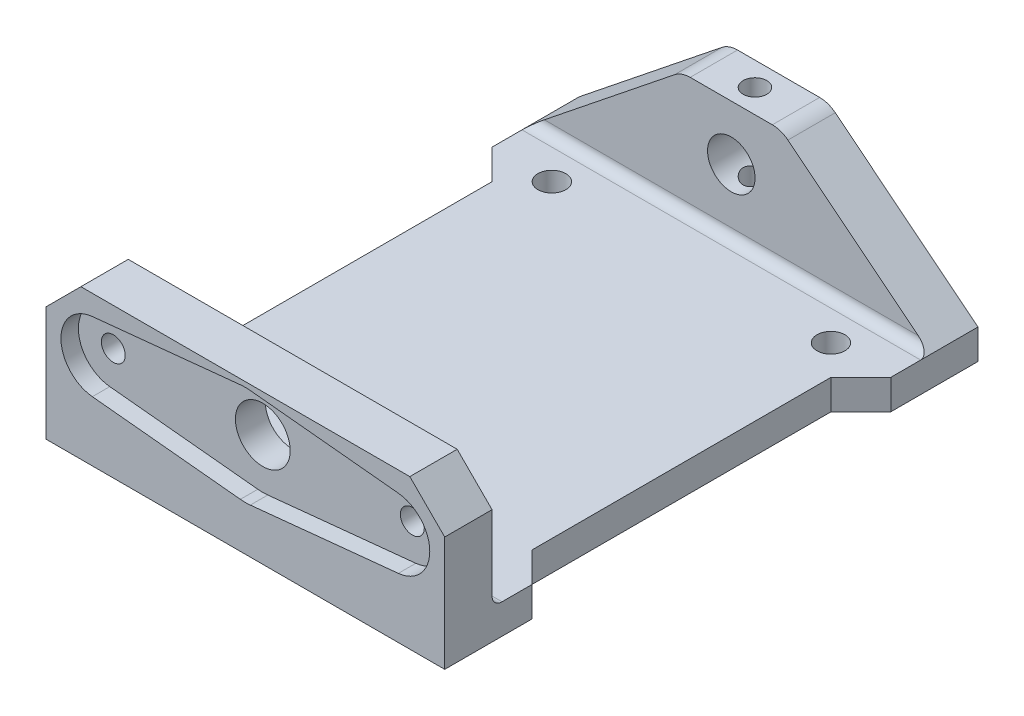
SolidWorks part; units mm, degrees
ref_plane "Front Plane" through (0, 0, 0) normal (0, 0, 1) x (1, 0, 0)
ref_plane "Top Plane" through (0, 0, 0) normal (0, 1, 0) x (1, 0, 0)
ref_plane "Right Plane" through (0, 0, 0) normal (1, 0, 0) x (0, 0, -1)
sketch "Sketch1" plane through (0, 0, 0) normal (0, 1, 0) x (1, 0, 0)
  line L1 (-14, 18) -> (14, 18)
  line L2 (-14, 18) -> (-14, -18)
  line L3 (-14, -18) -> (14, -18)
  line L4 (14, 18) -> (14, -18)
  line L5 (-14, 18) -> (14, -18) construction
  line L6 (-14, -18) -> (14, 18) construction
  line L7 (-20, 22) -> (20, 22)
  line L8 (-20, 22) -> (-20, -22)
  line L9 (-20, -22) -> (20, -22)
  line L10 (20, 22) -> (20, -22)
  line L11 (-20, 22) -> (20, -22) construction
  line L12 (-20, -22) -> (20, 22) construction
  circle A0 centre (-14, 18) radius 1.4
  circle A1 centre (14, 18) radius 1.4
  circle A2 centre (-14, -18) radius 1.4
  circle A3 centre (14, -18) radius 1.4
  point P0 (0, 0)
  point P6 (0, 0)
  dimension "D3" = 2.8
  dimension "D4" = 2.8
  dimension "D5" = 2.8
  dimension "D6" = 2.8
  dimension "D1" = 36
  dimension "D2" = 28
  dimension "D7" = 40
  dimension "D8" = 44
extrude "Boss-Extrude1" add sketch "Sketch1" along normal blind 3 contours L10 L7 L8 L9 A3 L3 A2 L2 A0 L1 A1 L4 | A3 L4 A1 L1 A0 L2 A2 L3
sketch "Sketch2" plane through (0, 0, 22) normal (0, 0, 1) x (1, 0, 0)
  line L0 (20, 3) -> (20, 0) construction
  line L1 (-20, 0) -> (20, 0)
  line L2 (-20, 0) -> (-20, 15)
  line L3 (-20, 15) -> (20, 15)
  line L4 (20, 0) -> (20, 15)
  dimension "D1" = 15
extrude "Boss-Extrude2" add sketch "Sketch2" along normal blind 4.75
sketch "Sketch3" plane through (0, 0, -22) normal (0, 0, -1) x (-1, 0, 0)
  line L1 (-20, 0) -> (20, 0)
  line L2 (-20, 0) -> (-20, 15)
  line L3 (-20, 15) -> (20, 15)
  line L4 (20, 0) -> (20, 15)
extrude "Boss-Extrude3" add sketch "Sketch3" along normal blind 4.75
sketch "Sketch4" plane through (0, 0, 26.75) normal (0, 0, 1) x (1, 0, 0)
  line L0 (-20, 9.5) -> (20, 9.5) construction
  line L1 (-20, 15) -> (-20, 0) construction
  line L2 (20, 0) -> (20, 15) construction
  line L3 (20, 15) -> (-20, 15) construction
  line L4 (-15.25, 11.9875) -> (-0.4, 13.4799)
  line L5 (-15.25, 7.0125) -> (-0.4, 5.5201)
  line L6 (0.4, 5.5201) -> (15.25, 7.0125)
  line L7 (15.25, 11.9875) -> (0.4, 13.4799)
  line L8 (15.35, 12.9825) -> (0.5, 14.4749)
  line L9 (-15.35, 12.9825) -> (-0.5, 14.4749)
  line L10 (-15.35, 6.0175) -> (-0.5, 4.5251)
  line L11 (0.5, 4.5251) -> (15.35, 6.0175)
  arc A0 (0.4, 13.4799) -> (-0.4, 13.4799) centre (0, 9.5) ccw
  arc A1 (15.25, 7.0125) -> (15.25, 11.9875) centre (15, 9.5) ccw
  arc A2 (-15.25, 11.9875) -> (-15.25, 7.0125) centre (-15, 9.5) ccw
  arc A3 (-0.4, 5.5201) -> (0.4, 5.5201) centre (0, 9.5) ccw
  arc A4 (15.35, 6.0175) -> (15.35, 12.9825) centre (15, 9.5) ccw
  arc A5 (0.5, 14.4749) -> (-0.5, 14.4749) centre (0, 9.5) ccw
  arc A6 (-15.35, 12.9825) -> (-15.35, 6.0175) centre (-15, 9.5) ccw
  arc A7 (-0.5, 4.5251) -> (0.5, 4.5251) centre (0, 9.5) ccw
  dimension "D2" = 8
  dimension "D3" = 5
  dimension "D4" = 5
  dimension "D1" = 5.5
  dimension "D5" = 15
  dimension "D6" = 15
  dimension "D7" = 1
extrude "Cut-Extrude1" cut sketch "Sketch4" against normal blind 1.75 contours A6 L0 A2 L4 A0 L7 A1 A4 L8 A5 L9 | L0 A6 L10 A7 L11 A4 A1 L6 A3 L5 A2 | L0 A2 L5 A3 L6 A1 | A2 L0 A1 L7 A0 L4
sketch "Sketch5" plane through (0, 0, 25) normal (0, 0, 1) x (1, 0, 0)
  line L0 (-15, 9.5) -> (15, 9.5) construction
  circle A0 centre (-15, 9.5) radius 1.2
  circle A1 centre (15, 9.5) radius 1.2
  circle A2 centre (0, 9.5) radius 2.75
  dimension "D1" = 2.4
  dimension "D2" = 2.4
  dimension "D3" = 5.5
extrude "Cut-Extrude2" cut sketch "Sketch5" against normal up to next
sketch "Sketch6" plane through (0, 0, -26.75) normal (0, 0, -1) x (-1, 0, 0)
  line L0 (-20, 9.5) -> (20, 9.5) construction
  line L1 (-20, 15) -> (-20, 0) construction
  line L2 (20, 0) -> (20, 15) construction
  line L3 (20, 15) -> (-20, 15) construction
  circle A0 centre (0, 9.5) radius 2.3813
  dimension "D2" = 4.7625
  dimension "D1" = 5.5
extrude "Cut-Extrude3" cut sketch "Sketch6" against normal up to next
sketch "Sketch7" plane through (0, 15, 0) normal (0, 1, 0) x (1, 0, 0)
  line L0 (-20, 24.375) -> (20, 24.375) construction
  line L1 (-20, 26.75) -> (-20, 22) construction
  line L2 (20, 26.75) -> (20, 22) construction
  circle A0 centre (0, 24.375) radius 1.1906
  dimension "D1" = 2.3813
extrude "Cut-Extrude4" cut sketch "Sketch7" against normal through all
sketch "Sketch8" plane through (0, 3, 0) normal (0, 1, 0) x (1, 0, 0)
  line L0 (0, 22) -> (0, -22) construction
  line L1 (-20, 22) -> (20, 22) construction
  line L2 (20, -22) -> (-20, -22) construction
  line L3 (-20, 0) -> (20, 0) construction
  line L4 (-20, 22) -> (-20, -22) construction
  line L5 (20, 22) -> (20, -22) construction
  line L6 (-20, 18) -> (-17, 15)
  line L7 (-17, 15) -> (-17, -15)
  line L8 (-17, -15) -> (-20, -18)
  line L9 (-20, -18) -> (-20, 18)
  line L10 (17, -15) -> (20, -18)
  line L11 (17, 15) -> (17, -15)
  line L12 (20, 18) -> (17, 15)
  line L13 (20, -18) -> (20, 18)
  point P14 (-17, 0)
  dimension "D1" = 45
  dimension "D2" = 45
  dimension "D3" = 3
  dimension "D4" = 30
extrude "Cut-Extrude5" cut sketch "Sketch8" against normal up to next
sketch "Sketch9" plane through (0, 0, -26.75) normal (0, 0, -1) x (-1, 0, 0)
  line L0 (-20, 15) -> (-4.995, 15)
  line L1 (20, 15) -> (-20, 15) construction
  line L2 (-4.995, 15) -> (-20, 3)
  line L3 (-20, 15) -> (-20, 0) construction
  line L4 (-20, 3) -> (-20, 15)
  line L5 (20, 15) -> (5, 15)
  line L6 (5, 15) -> (20, 3)
  line L7 (20, 0) -> (20, 15) construction
  line L8 (20, 3) -> (20, 15)
  dimension "D1" = 15.005
  dimension "D2" = 12
  dimension "D3" = 15
  dimension "D4" = 12
extrude "Cut-Extrude6" cut sketch "Sketch9" against normal up to next
fillet "Fillet1" radius 1 2 edges at (0, 3, 22) (0, 3, -22)
chamfer "Chamfer1" distance 3.5 2 edges at (-20, 15, 24.375) (20, 15, 24.375)
fillet "Fillet2" radius 2.5 2 edges at (-5, 15, -24.375) (4.995, 15, -24.375)
